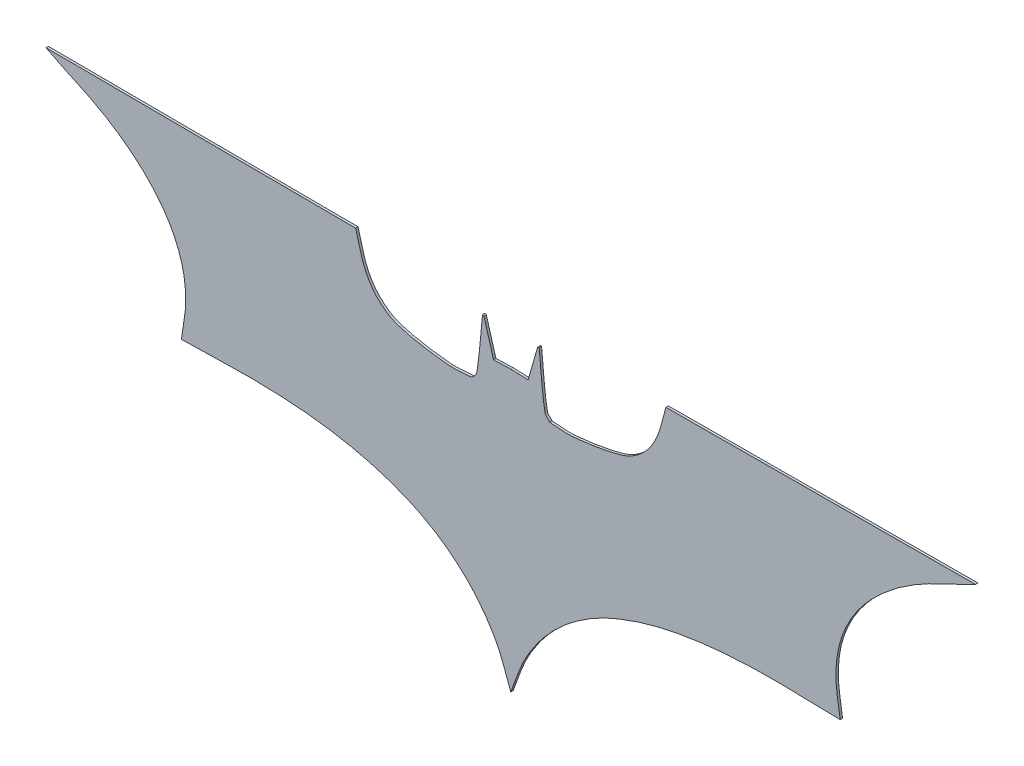
SolidWorks part; units mm, degrees
ref_plane "Ön Düzlem" through (0, 0, 0) normal (0, 0, 1) x (1, 0, 0)
ref_plane "Üst Düzlem" through (0, 0, 0) normal (0, 1, 0) x (1, 0, 0)
ref_plane "Sağ Düzlem" through (0, 0, 0) normal (1, 0, 0) x (0, 0, -1)
sketch "Sketch1" plane through (0, 0, 0) normal (0, 0, 1) x (1, 0, 0)
  line L0 (331.1667, 368) -> (1655.8333, 368) construction
  line L1 (24, 709) -> (669, 706)
  line L2 (933, 682) -> (936, 681)
  line L3 (936, 681) -> (956, 612)
  line L4 (956, 612) -> (992, 613.3846)
  line L5 (1028, 612) -> (992, 613.3846)
  line L6 (1048, 681) -> (1028, 612)
  line L7 (1051, 682) -> (1048, 681)
  line L9 (1960, 709) -> (1315, 706)
  spline S0 degree 3 poles (669, 706) (675.6667, 684) (679.4287, 660.9006) (689, 640) (695.9698, 624.7802) (705.7393, 610.3973) (718, 599) (729.933, 587.9073) (744.4068, 578.7219) (760, 574) (792.4154, 564.1841) (826.3195, 559.5688) (860, 556) (876.9184, 554.2073) (894, 557.3333) (911, 558) knots 0 0 0 0 1 1 1 2 2 2 3 3 3 4 4 4 5 5 5 5
  spline S1 degree 3 poles (911, 558) (914.3333, 562.3333) (920.045, 565.617) (921, 571) (927.5012, 607.6433) (929, 645) (933, 682) knots 0 0 0 0 1 1 1 2 2 2 2
  spline S2 degree 3 poles (1073, 558) (1069.6667, 562.3333) (1063.955, 565.617) (1063, 571) (1056.4988, 607.6433) (1055, 645) (1051, 682) knots 0 0 0 0 1 1 1 2 2 2 2
  spline S3 degree 3 poles (1315, 706) (1308.3333, 684) (1304.5713, 660.9006) (1295, 640) (1288.0302, 624.7802) (1278.2607, 610.3973) (1266, 599) (1254.067, 587.9073) (1239.5932, 578.7219) (1224, 574) (1191.5846, 564.1841) (1157.6805, 559.5688) (1124, 556) (1107.0816, 554.2073) (1090, 557.3333) (1073, 558) knots 0 0 0 0 1 1 1 2 2 2 3 3 3 4 4 4 5 5 5 5
  spline S4 degree 3 poles (1678, 324) (1675, 349.3333) (1668.8228, 374.4903) (1669, 400) (1669.1591, 422.9099) (1672.1478, 446.1382) (1679, 468) (1686.3125, 491.3303) (1697.3267, 513.7313) (1711, 534) (1725.9237, 556.1222) (1744.1416, 576.1743) (1764, 594) (1786.7239, 614.3978) (1811.7022, 632.48) (1838, 648) (1877.1563, 671.1086) (1919.9679, 687.4442) (1960, 709) knots 0 0 0 0 1 1 1 2 2 2 3 3 3 4 4 4 5 5 5 6 6 6 6
  spline S5 degree 3 poles (992, 31) (982, 56) (974.715, 82.2654) (962, 106) (949.5559, 129.229) (934.3413, 151.1575) (917, 171) (899.4559, 191.0745) (879.5402, 209.2902) (858, 225) (834.9503, 241.8107) (810.1128, 256.5104) (784, 268) (751.4852, 282.3065) (717.5422, 293.7099) (683, 302) (642.2886, 311.7707) (600.7062, 318.3287) (559, 322) (504.8597, 326.7659) (450.3214, 327.7523) (396, 326) (366.0082, 325.0325) (336, 324.6667) (306, 324) knots 0 0 0 0 1 1 1 2 2 2 3 3 3 4 4 4 5 5 5 6 6 6 7 7 7 8 8 8 8
  spline S6 degree 3 poles (306, 324) (309, 349.3333) (315.1772, 374.4903) (315, 400) (314.8409, 422.9099) (311.8522, 446.1382) (305, 468) (297.6875, 491.3303) (286.6733, 513.7313) (273, 534) (258.0763, 556.1222) (239.8584, 576.1743) (220, 594) (197.2761, 614.3978) (172.2978, 632.48) (146, 648) (106.8437, 671.1086) (64.0321, 687.4442) (24, 709) knots 0 0 0 0 1 1 1 2 2 2 3 3 3 4 4 4 5 5 5 6 6 6 6
  spline S7 degree 3 poles (992, 31) (1002, 56) (1009.285, 82.2654) (1022, 106) (1034.4441, 129.229) (1049.6587, 151.1575) (1067, 171) (1084.5441, 191.0745) (1104.4598, 209.2902) (1126, 225) (1149.0497, 241.8107) (1173.8872, 256.5104) (1200, 268) (1232.5148, 282.3065) (1266.4578, 293.7099) (1301, 302) (1341.7114, 311.7707) (1383.2938, 318.3287) (1425, 322) (1479.1403, 326.7659) (1533.6786, 327.7523) (1588, 326) (1617.9918, 325.0325) (1648, 324.6667) (1678, 324) knots 0 0 0 0 1 1 1 2 2 2 3 3 3 4 4 4 5 5 5 6 6 6 7 7 7 8 8 8 8
extrude "Boss-Extrude1" add sketch "Sketch1" along normal blind 5
